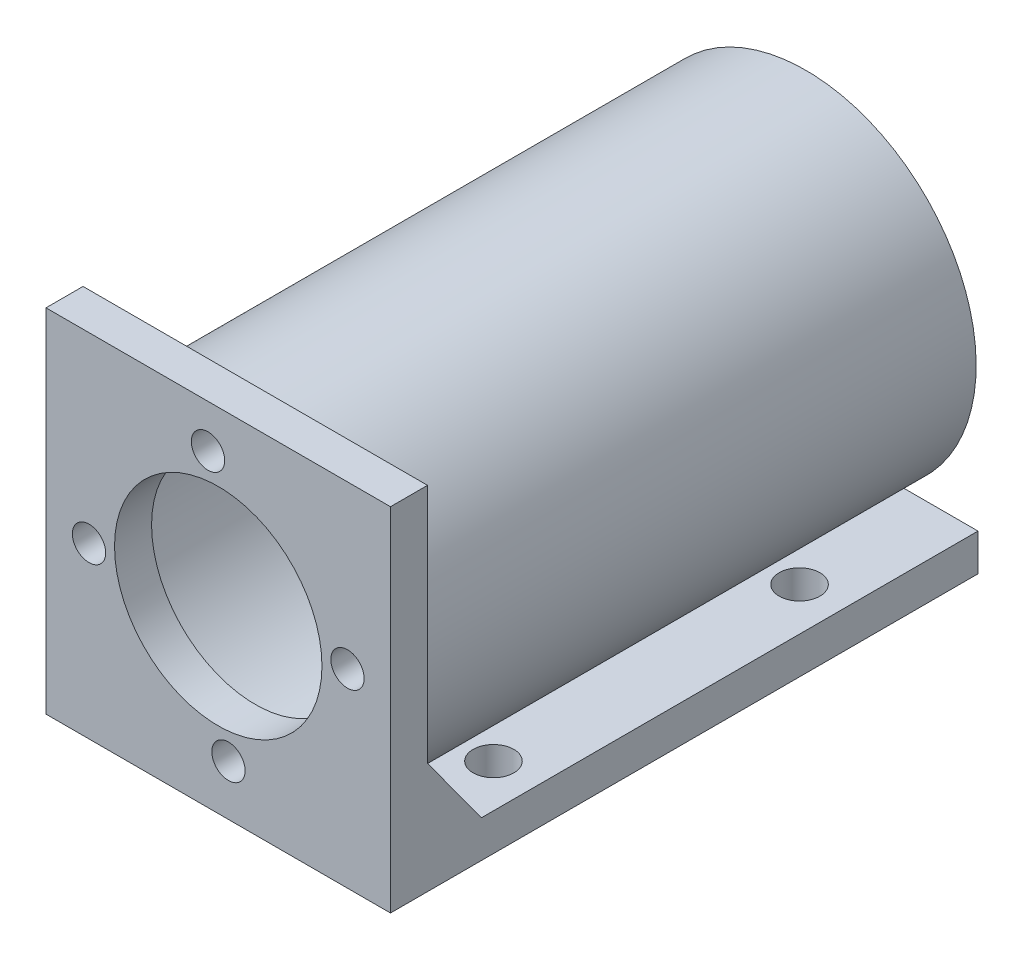
SolidWorks part; units mm, degrees
ref_plane "Front Plane" through (0, 0, 0) normal (0, 0, 1) x (1, 0, 0)
ref_plane "Top Plane" through (0, 0, 0) normal (0, 1, 0) x (1, 0, 0)
ref_plane "Right Plane" through (0, 0, 0) normal (1, 0, 0) x (0, 0, -1)
sketch "Sketch1" plane through (0, 0, 0) normal (0, 0, 1) x (1, 0, 0)
  line L0 (0, 0) -> (-28.1103, 0) construction
  line L1 (-23.25, 23.25) -> (23.25, 23.25)
  line L2 (-23.25, 23.25) -> (-23.25, -23.25)
  line L3 (-23.25, -23.25) -> (23.25, -23.25)
  line L4 (23.25, 23.25) -> (23.25, -23.25)
  line L5 (-23.25, 23.25) -> (23.25, -23.25) construction
  line L6 (-23.25, -23.25) -> (23.25, 23.25) construction
  line L7 (-12.3744, 12.3744) -> (0, 0)
  circle A0 centre (0, 0) radius 23.25
  circle A1 centre (0, 0) radius 17.5
  circle A6 centre (0, 0) radius 14
  circle A7 centre (-1.382, 17.4453) radius 2.25
  circle A8 centre (17.4453, 1.382) radius 2.25
  circle A9 centre (1.382, -17.4453) radius 2.25
  circle A10 centre (-17.4453, -1.382) radius 2.25
  point P6 (0, 23.25)
  point P15 (0, 0)
  point P20 (0, 0)
  point P32 (0, 0)
  dimension "D1" = 46.5
  dimension "D2" = 35
  dimension "D7" = 28
  dimension "D8" = 4.5
  dimension "D5" = 23.25
  dimension "D4" = 23.25
  dimension "D9" = 4
extrude "Boss-Extrude1" add sketch "Sketch1" along normal blind 5
sketch "Sketch2" plane through (0, 0, 0) normal (0, 0, -1) x (-1, 0, 0)
  line L0 (23.25, 23.25) -> (23.25, -23.25) construction
  line L1 (-23.25, -19.25) -> (23.25, -19.25)
  line L2 (-23.25, -19.25) -> (-23.25, -24.25)
  line L3 (-23.25, -24.25) -> (23.25, -24.25)
  line L4 (23.25, -19.25) -> (23.25, -24.25)
  line L5 (-23.25, -19.25) -> (23.25, -24.25) construction
  line L6 (-23.25, -24.25) -> (23.25, -19.25) construction
  line L7 (23.25, -23.25) -> (-23.25, -23.25) construction
  point P0 (0, -21.75)
  dimension "D1" = 5
  dimension "D2" = 46.5
  dimension "D3" = 0
  dimension "D4" = 1
extrude "Boss-Extrude2" add sketch "Sketch2" along normal blind 149
sketch "Sketch4" plane through (0, -23.25, 0) normal (0, -1, 0) x (1, 0, 0)
  line L0 (23.25, 5) -> (23.25, 0) construction
  line L1 (-23.25, 5) -> (-23.25, 0) construction
  line L2 (-23.25, 5) -> (23.25, 5) construction
  line L3 (-23.25, 0) -> (23.25, 0) construction
  line L4 (23.25, 5) -> (23.25, 0)
  line L5 (-23.25, 5) -> (-23.25, 0)
  line L6 (-23.25, 5) -> (23.25, 5)
  line L7 (-23.25, 0) -> (23.25, 0)
extrude "Boss-Extrude3" add sketch "Sketch4" along normal up to surface (1 mm away) up to face at (0, -24.25, -74.5)
sketch "Sketch5" plane through (0, -19.25, 0) normal (0, 1, 0) x (1, 0, 0)
  circle A0 centre (17.4431, 14.7088) radius 2.75
  circle A1 centre (17.4431, 87.8337) radius 2.75
  circle A2 centre (17.4431, 56.0212) radius 2.75
  circle A3 centre (17.4431, 129.1407) radius 2.75
  dimension "D1" = 5.5
  dimension "D2" = 5.5
  dimension "D3" = 5.5
  dimension "D4" = 5.5
extrude "Cut-Extrude1" cut sketch "Sketch5" against normal blind 10
mirror "Mirror1" about plane through (0, 0, 0) normal (1, 0, 0) of "Cut-Extrude1"
sketch "Sketch9" plane through (0, 0, -149) normal (0, 0, -1) x (-1, 0, 0)
  circle A0 centre (0, 0) radius 23
  dimension "D1" = 46
extrude "Cut-Extrude2" cut sketch "Sketch9" against normal up to surface (149 mm away) up to face at (14, 0, 0)
sketch "Sketch10" plane through (0, 0, -149) normal (0, 0, -1) x (-1, 0, 0)
  circle A0 centre (0, 0) radius 23
  circle A1 centre (0, 0) radius 21
  dimension "D1" = 46
  dimension "D2" = 42
extrude "Boss-Extrude4" add sketch "Sketch10" against normal blind 149
chamfer "Chamfer1" distance 10 angle 36 1 edges at (17.9186, -19.25, 0)
chamfer "Chamfer2" distance 10 angle 36 1 edges at (-17.9186, -19.25, 0)
sketch "Sketch11" plane through (0, -24.25, 0) normal (0, -1, 0) x (1, 0, 0)
  line L0 (23.25, -149) -> (-23.25, -149) construction
  line L1 (23.25, -149) -> (-23.25, -149)
  line L2 (23.25, -149) -> (23.25, -74.3053)
  line L3 (23.25, -74.3053) -> (-23.25, -74.3053)
  line L4 (-23.25, -149) -> (-23.25, -74.3053)
  line L5 (23.25, -149) -> (23.25, 5) construction
  line L6 (-23.25, -149) -> (-23.25, 5) construction
  dimension "D1" = 0
extrude "Cut-Extrude3" cut sketch "Sketch11" against normal blind 149
